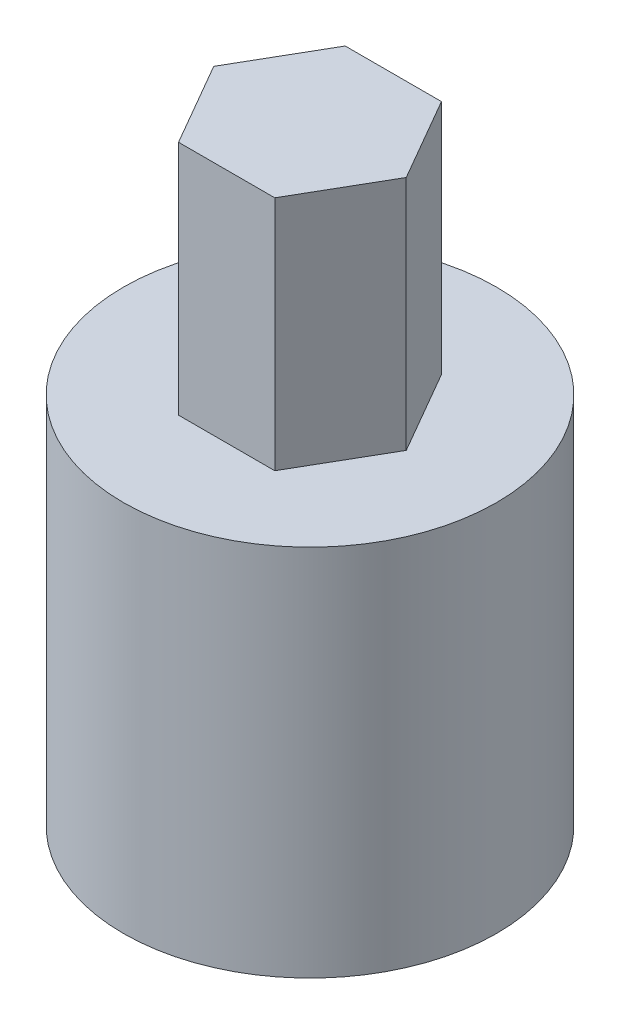
SolidWorks part; units mm, degrees
ref_plane "Front Plane" through (0, 0, 0) normal (0, 0, 1) x (1, 0, 0)
ref_plane "Top Plane" through (0, 0, 0) normal (0, 1, 0) x (1, 0, 0)
ref_plane "Right Plane" through (0, 0, 0) normal (1, 0, 0) x (0, 0, -1)
sketch "Sketch1" plane through (0, 0, 0) normal (0, 1, 0) x (1, 0, 0)
  circle A1 centre (0, 0) radius 7.5
  dimension "D1" = 15
extrude "Boss-Extrude1" add sketch "Sketch1" along normal blind 15
sketch "Sketch4" plane through (0, 15, 0) normal (0, 1, 0) x (1, 0, 0)
  line L1 (1.9341, 3.35) -> (-1.9341, 3.35)
  line L2 (-1.9341, 3.35) -> (-3.8682, 0)
  line L3 (-3.8682, 0) -> (-1.9341, -3.35)
  line L4 (-1.9341, -3.35) -> (1.9341, -3.35)
  line L5 (1.9341, -3.35) -> (3.8682, 0)
  line L6 (3.8682, 0) -> (1.9341, 3.35)
  circle A0 centre (0, 0) radius 3.35 construction
  dimension "D1" = 6.7
extrude "Boss-Extrude2" add sketch "Sketch4" along normal blind 9.5
sketch "Sketch5" plane through (0, 0, 0) normal (0, -1, 0) x (1, 0, 0)
  line L0 (-1.6962, 2.627) -> (1.6962, 2.627)
  circle A0 centre (0, 0) radius 3.127
  dimension "D1" = 6.254
  dimension "D2" = 2.627
extrude "Cut-Extrude1" cut sketch "Sketch5" against normal blind 12 contours L0 A0
equation "\"D2@Sketch5\"=2.5+0.005in"
equation "\"D1@Sketch5\"=6+0.01in"
